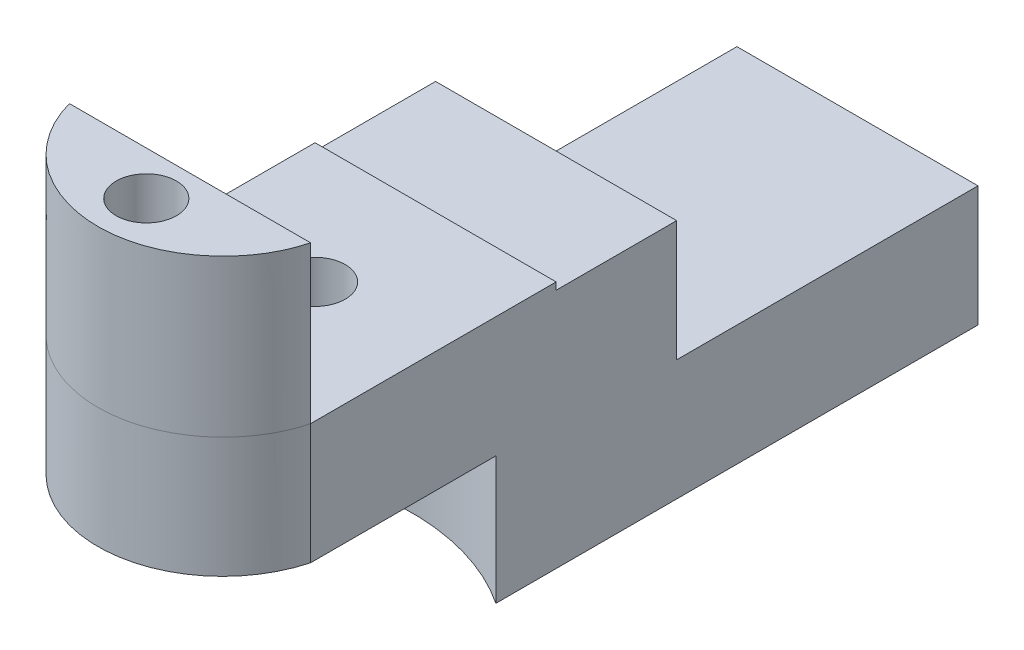
SolidWorks part; units mm, degrees
ref_plane "Front Plane" through (0, 0, 0) normal (0, 0, 1) x (1, 0, 0)
ref_plane "Top Plane" through (0, 0, 0) normal (0, 1, 0) x (1, 0, 0)
ref_plane "Right Plane" through (0, 0, 0) normal (1, 0, 0) x (0, 0, -1)
sketch "Sketch1" plane through (0, 0, 0) normal (0, 1, 0) x (1, 0, 0)
  line L0 (0, 3.81) -> (0, -3.81) construction
  line L1 (1.27, -3.81) -> (-1.27, -3.81)
  line L2 (2.54, -2.54) -> (2.54, 3.81)
  line L3 (2.54, 3.81) -> (-2.54, 3.81)
  line L4 (-2.54, -2.54) -> (-2.54, 3.81)
  line L5 (2.54, -3.81) -> (-2.54, 3.81) construction
  line L6 (2.54, 3.81) -> (-2.54, -3.81) construction
  arc A0 (1.27, -3.81) -> (2.54, -2.54) centre (1.27, -2.54) ccw
  arc A1 (-1.27, -3.81) -> (-2.54, -2.54) centre (-1.27, -2.54) cw
  circle A2 centre (0, 2.54) radius 0.635
  circle A3 centre (0, -1.016) radius 0.635
  point P0 (0, 0)
  dimension "D3" = 1.27
  dimension "D4" = 1.27
  dimension "D6" = 1.27
  dimension "D1" = 5.08
  dimension "D2" = 7.62
  dimension "D5" = 2.54
  dimension "D7" = 3.556
extrude "Boss-Extrude1" add sketch "Sketch1" along normal blind 2.54
sketch "Sketch3" plane through (0, 2.54, 0) normal (0, 1, 0) x (1, 0, 0)
  line L0 (-2.54, 3.81) -> (-2.54, -2.54) construction
  line L1 (2.54, -2.54) -> (2.54, 3.81) construction
  line L2 (-2.54, -0.0958) -> (-2.6943, -4.6455)
  line L3 (-2.6943, -4.6455) -> (2.54, -5.1941)
  line L4 (2.54, -5.1941) -> (2.54, -0.0958)
  arc A0 (-2.54, -0.0958) -> (2.54, -0.0958) centre (0, 0.592) ccw
extrude "Cut-Extrude1" cut sketch "Sketch3" against normal blind 5.08 and the other way blind 2.54
sketch "Sketch4" plane through (0, 2.54, 0) normal (0, 1, 0) x (1, 0, 0)
  line L0 (-2.54, -0.0958) -> (2.54, -0.0958)
  line L1 (0, -0.381) -> (0, -1.651) construction
  line L2 (-0.635, -1.016) -> (0.635, -1.016) construction
  arc A0 (-2.54, -0.0958) -> (2.54, -0.0958) centre (0, 0.592) ccw construction
  circle A1 centre (0, -1.016) radius 0.635 construction
  circle A2 centre (0, -1.016) radius 0.635
  spline S0 degree 3 poles (-2.54, -0.0958) (-2.3762, -0.7151) (-1.6534, -1.7018) (-0.1577, -2.1373) (1.4792, -1.8181) (2.343, -0.8817) (2.54, -0.0958) knots 0 0 0 0 0.281857 0.499579 0.64729 1 1 1 1
extrude "Boss-Extrude2" add sketch "Sketch4" along normal blind 3.302
sketch "Sketch5" plane through (0, 0, -3.81) normal (0, 0, -1) x (-1, 0, 0)
  line L1 (2.54, 2.54) -> (-2.54, 2.54)
  line L2 (2.54, 2.54) -> (2.54, 0)
  line L3 (2.54, 0) -> (-2.54, 0)
  line L4 (-2.54, 2.54) -> (-2.54, 0)
extrude "Boss-Extrude3" add sketch "Sketch5" along normal blind 1.27
sketch "Sketch6" plane through (0, 0, 0) normal (0, -1, 0) x (-1, 0, 0)
  line L0 (-2.54, 3.81) -> (-2.54, 5.08)
  line L1 (-2.54, -0.0958) -> (-2.54, 5.08) construction
  line L2 (2.54, 5.08) -> (2.54, -0.0958) construction
  line L4 (2.54, 5.08) -> (2.54, 3.81)
  line L5 (-2.54, 3.81) -> (2.54, 3.81) construction
  line L6 (-2.54, 3.81) -> (-2.54, 5.08)
  line L7 (-2.54, 5.08) -> (2.54, 5.08)
  line L8 (2.54, 3.81) -> (2.54, 5.08)
  arc A0 (-2.54, 3.81) -> (2.54, 3.81) centre (0, 0) cw
  line M10 (2.54, -0.0958) -> (2.54, 5.08)
  line M11 (2.54, 5.08) -> (-2.54, 5.08)
  line M12 (-2.54, 5.08) -> (-2.54, -0.0958)
extrude "Boss-Extrude4" add sketch "Sketch6" along normal blind 2.6918 contours A0 M12 M10 M11
sketch "Sketch7" plane through (0, 0, -5.08) normal (0, 0, -1) x (-1, 0, 0)
  line L0 (2.54, -2.6918) -> (2.54, 2.54) construction
  line L1 (-2.54, 2.54) -> (2.54, 2.54) construction
  line L2 (-2.54, 2.54) -> (-2.54, 2.3882) construction
  line L3 (-2.54, 2.3882) -> (2.54, 2.3882) construction
  line L4 (2.54, 2.54) -> (2.54, 2.3882) construction
  line L6 (-2.54, -2.6918) -> (2.54, -2.6918)
  line L7 (-2.54, -2.6918) -> (-2.54, 2.3882)
  line L8 (-2.54, 2.3882) -> (2.54, 2.3882)
  line L9 (2.54, -2.6918) -> (2.54, 2.3882)
extrude "Boss-Extrude6" add sketch "Sketch7" along normal blind 2.54
sketch "Sketch8" plane through (0, 0, -7.62) normal (0, 0, -1) x (-1, 0, 0)
  line L0 (2.54, -2.6918) -> (2.54, 2.3882) construction
  line L1 (-2.54, -2.6918) -> (2.54, -2.6918)
  line L2 (-2.54, -2.6918) -> (-2.54, -0.1518)
  line L3 (-2.54, -0.1518) -> (2.54, -0.1518)
  line L4 (2.54, -2.6918) -> (2.54, -0.1518)
  dimension "D1" = 2.54
extrude "Boss-Extrude7" add sketch "Sketch8" along normal blind 6.35
